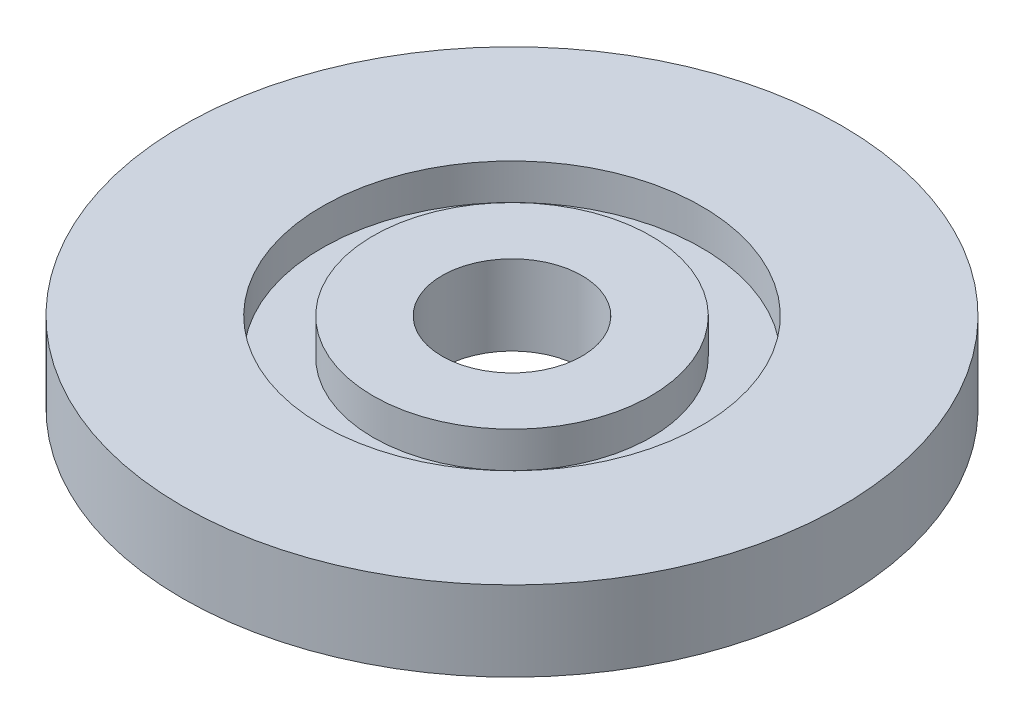
SolidWorks part; units mm, degrees
material "ABS"
ref_plane "Front Plane" through (0, 0, 0) normal (0, 0, 1) x (1, 0, 0)
ref_plane "Top Plane" through (0, 0, 0) normal (0, 1, 0) x (1, 0, 0)
ref_plane "Right Plane" through (0, 0, 0) normal (1, 0, 0) x (0, 0, -1)
sketch "Sketch1" plane through (0, 0, 0) normal (0, 1, 0) x (1, 0, 0)
  circle A0 centre (0, 0) radius 82.5
  dimension "D1" = 165
extrude "Boss-Extrude1" add sketch "Sketch1" along normal blind 20
sketch "Sketch2" plane through (0, 20, 0) normal (0, 1, 0) x (1, 0, 0)
  circle A0 centre (0, 0) radius 17.5
  dimension "D1" = 35
extrude "Cut-Extrude1" cut sketch "Sketch2" against normal blind 20
sketch "Sketch3" plane through (0, 20, 0) normal (0, 1, 0) x (1, 0, 0)
  circle A0 centre (0, 0) radius 47.5
  circle A1 centre (0, 0) radius 34.75
  dimension "D1" = 95
  dimension "D2" = 69.5
extrude "Cut-Extrude2" cut sketch "Sketch3" against normal blind 9
sketch "Sketch4" plane through (0, 0, 0) normal (0, -1, 0) x (1, 0, 0)
  circle A0 centre (0, 70) radius 2.5
  circle A1 centre (60.6218, 35) radius 2.5
  circle A2 centre (60.6218, -35) radius 2.5
  circle A3 centre (0, -70) radius 2.5
  circle A4 centre (-60.6218, -35) radius 2.5
  circle A5 centre (-60.6218, 35) radius 2.5
  point P12 (0, 0)
  point P16 (0, 0)
  dimension "D1" = 5
  dimension "D2" = 70
  dimension "D3" = 6
extrude "Cut-Extrude3" cut sketch "Sketch4" against normal blind 13
